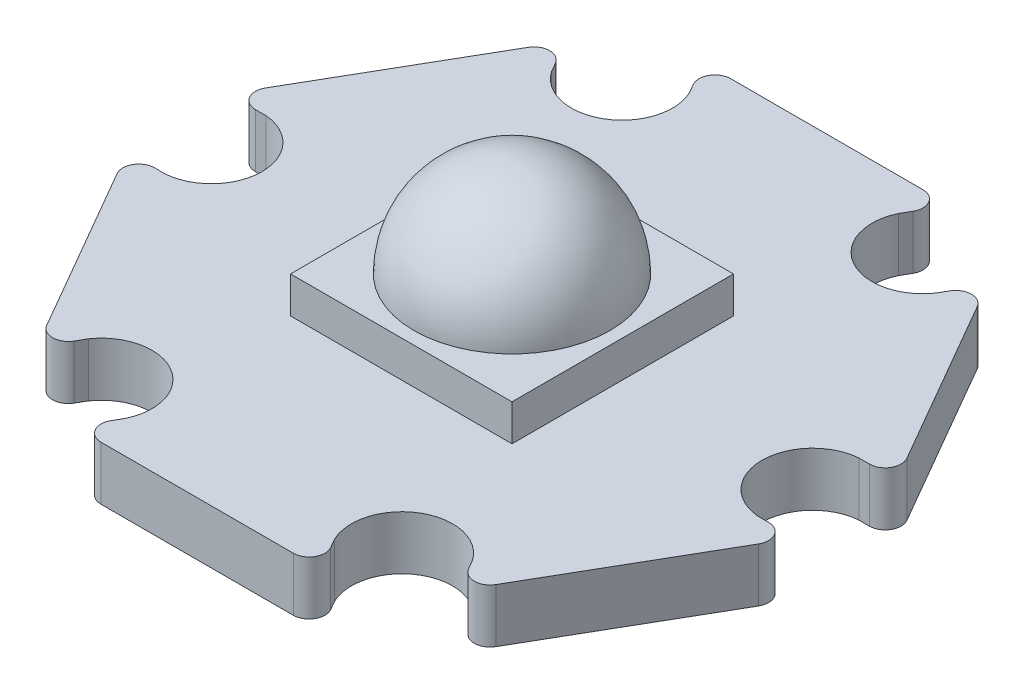
SolidWorks part; units mm, degrees
ref_plane "Front Plane" through (0, 0, 0) normal (0, 0, 1) x (1, 0, 0)
ref_plane "Top Plane" through (0, 0, 0) normal (0, 1, 0) x (1, 0, 0)
ref_plane "Right Plane" through (0, 0, 0) normal (1, 0, 0) x (0, 0, -1)
sketch "Sketch1" plane through (0, 0, 0) normal (0, 1, 0) x (1, 0, 0)
  line L0 (-9.95, 0) -> (9.95, 0) construction
  line L1 (6.6651, -8.3557) -> (10.5688, -1.5943)
  line L2 (10.5688, 1.5943) -> (6.6651, 8.3557)
  line L3 (3.9037, 9.95) -> (-3.9037, 9.95)
  line L4 (-6.6651, 8.3557) -> (-10.5688, 1.5943)
  line L5 (-10.5688, -1.5943) -> (-6.6651, -8.3557)
  line L6 (-3.9037, -9.95) -> (3.9037, -9.95)
  line L7 (-4.975, -8.617) -> (4.975, 8.617) construction
  line L8 (-4.975, 8.617) -> (4.975, -8.617) construction
  line L9 (-6.0634, -7.3134) -> (-6.6651, -8.3557)
  line L10 (-3.3019, -8.9077) -> (-3.9037, -9.95)
  line L11 (-9.3653, 1.5943) -> (-10.5688, 1.5943)
  line L12 (-9.3653, -1.5943) -> (-10.5688, -1.5943)
  line L13 (-3.3019, 8.9077) -> (-3.9037, 9.95)
  line L14 (-6.0634, 7.3134) -> (-6.6651, 8.3557)
  line L15 (6.0634, 7.3134) -> (6.6651, 8.3557)
  line L16 (3.3019, 8.9077) -> (3.9037, 9.95)
  line L17 (9.3653, -1.5943) -> (10.5688, -1.5943)
  line L18 (9.3653, 1.5943) -> (10.5688, 1.5943)
  line L19 (3.3019, -8.9077) -> (3.9037, -9.95)
  line L20 (6.0634, -7.3134) -> (6.6651, -8.3557)
  circle A0 centre (0, 0) radius 9.95 construction
  circle A1 centre (0, 0) radius 9.5 construction
  arc A2 (-3.3019, -8.9077) -> (-6.0634, -7.3134) centre (-4.75, -8.2272) ccw
  arc A3 (-9.3653, -1.5943) -> (-9.3653, 1.5943) centre (-9.5, 0) ccw
  arc A4 (-6.0634, 7.3134) -> (-3.3019, 8.9077) centre (-4.75, 8.2272) ccw
  arc A5 (3.3019, 8.9077) -> (6.0634, 7.3134) centre (4.75, 8.2272) ccw
  arc A6 (9.3653, 1.5943) -> (9.3653, -1.5943) centre (9.5, 0) ccw
  arc A7 (6.0634, -7.3134) -> (3.3019, -8.9077) centre (4.75, -8.2272) ccw
  dimension "D2" = 19
  dimension "D3" = 3.2
  dimension "D1" = 19.9
  dimension "D4" = 6
extrude "Boss-Extrude1" add sketch "Sketch1" along normal blind 1.7
fillet "Fillet1" radius 0.5 12 edges at (-6.6651, 0.85, -8.3557) (-10.5688, 0.85, -1.5943) (-10.5688, 0.85, 1.5943) (-6.6651, 0.85, 8.3557) (-3.9037, 0.85, 9.95) (3.9037, 0.85, 9.95) (6.6651, 0.85, 8.3557) (10.5688, 0.85, 1.5943) (10.5688, 0.85, -1.5943) (6.6651, 0.85, -8.3557) (3.9037, 0.85, -9.95) (-3.9037, 0.85, -9.95)
sketch "Sketch4" plane through (0, 1.7, 0) normal (0, 1, 0) x (1, 0, 0)
  line L0 (-3.0377, -9.95) -> (3.0377, -9.95) construction
  line L1 (-3.5, -3.5) -> (3.5, -3.5)
  line L2 (-3.5, -3.5) -> (-3.5, 3.5)
  line L3 (-3.5, 3.5) -> (3.5, 3.5)
  line L4 (3.5, -3.5) -> (3.5, 3.5)
  line L5 (-3.5, 3.5) -> (3.5, -3.5) construction
  line L6 (-3.5, -3.5) -> (3.5, 3.5) construction
  dimension "D1" = 7
  dimension "D2" = 7
extrude "Boss-Extrude2" add sketch "Sketch4" along normal blind 1.15
sketch "Sketch5" plane through (0, 2.85, 0) normal (0, 1, 0) x (1, 0, 0)
  line L0 (0, 3.1) -> (0, -3.1)
  arc A0 (0, -3.1) -> (0, 3.1) centre (0, 0) ccw
  dimension "D1" = 6.2
revolve "Revolve4" add sketch "Sketch5" angle 180 about L0
sketch "Sketch6" plane through (0, 1.7, 0) normal (0, 1, 0) x (-1, 0, 0)
  line L0 (-3.5047, 9.7577) -> (-6.6991, 7.9134) construction
  line L1 (3.2877, -9.883) -> (6.9151, -7.7887) construction
  arc A0 (-3.0377, 9.95) -> (-3.4707, 9.2) centre (-3.0377, 9.45) ccw construction
  arc A2 (-6.2321, 7.6057) -> (-7.0981, 7.6057) centre (-6.6651, 7.3557) ccw construction
  arc A3 (6.2321, -7.6057) -> (7.0981, -7.6057) centre (6.6651, -7.3557) ccw construction
  arc A4 (3.0377, -9.95) -> (3.4707, -9.2) centre (3.0377, -9.45) ccw construction
